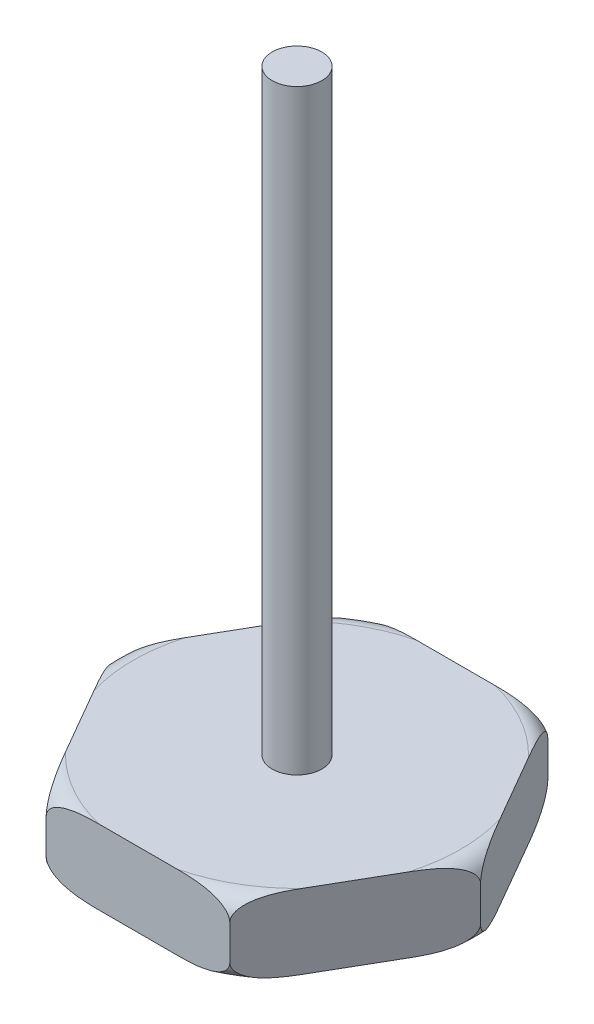
SolidWorks part; units mm, degrees
ref_plane "Front Plane" through (0, 0, 0) normal (0, 0, 1) x (1, 0, 0)
ref_plane "Top Plane" through (0, 0, 0) normal (0, 1, 0) x (1, 0, 0)
ref_plane "Right Plane" through (0, 0, 0) normal (1, 0, 0) x (0, 0, -1)
sketch "Sketch1" plane through (0, 0, 0) normal (0, 1, 0) x (1, 0, 0)
  line L1 (9.2376, 0) -> (4.6188, 8)
  line L2 (4.6188, 8) -> (-4.6188, 8)
  line L3 (-4.6188, 8) -> (-9.2376, 0)
  line L4 (-9.2376, 0) -> (-4.6188, -8)
  line L5 (-4.6188, -8) -> (4.6188, -8)
  line L6 (4.6188, -8) -> (9.2376, 0)
  circle A0 centre (0, 0) radius 8 construction
  point P1 (0, 0)
  dimension "D1" = 16
extrude "Boss-Extrude1" add sketch "Sketch1" along normal blind 3.75
sketch "Sketch2" plane through (0, 0, 0) normal (0, 0, 1) x (1, 0, 0)
  line L0 (9.2376, 3.75) -> (9.2376, 0) construction
  line L1 (4.6188, 3.75) -> (9.2376, 3.75) construction
  line L2 (9.2376, 2.75) -> (9.2376, 3.75)
  line L3 (9.2376, 3.75) -> (8.2376, 3.75)
  line L4 (0, 0) -> (0, 1.7533) construction
  line L5 (-4.6188, 0) -> (4.6188, 0) construction
  arc A0 (9.2376, 2.75) -> (8.2376, 3.75) centre (8.2376, 2.75) ccw
  dimension "D1" = 1
revolve "Cut-Revolve1" cut sketch "Sketch2" angle 360 about L4
sketch "Sketch3" plane through (0, 0, 0) normal (0, 0, 1) x (1, 0, 0)
  line L0 (4.6188, 0) -> (9.2376, 0) construction
  line L1 (9.2376, 2.75) -> (9.2376, 0) construction
  line L2 (9.2376, 0) -> (8.2376, 0)
  line L3 (9.2376, 0) -> (9.2376, 1)
  line L4 (0, 0) -> (0, 1.4498) construction
  arc A0 (9.2376, 1) -> (8.2376, 0) centre (8.2376, 1) cw
  dimension "D1" = 1
revolve "Cut-Revolve2" cut sketch "Sketch3" angle 360 about L4
sketch "Sketch4" plane through (0, 3.75, 0) normal (0, 1, 0) x (1, 0, 0)
  circle A0 centre (0, 0) radius 1.25
  dimension "D1" = 2.5
extrude "Boss-Extrude2" add sketch "Sketch4" along normal blind 30
